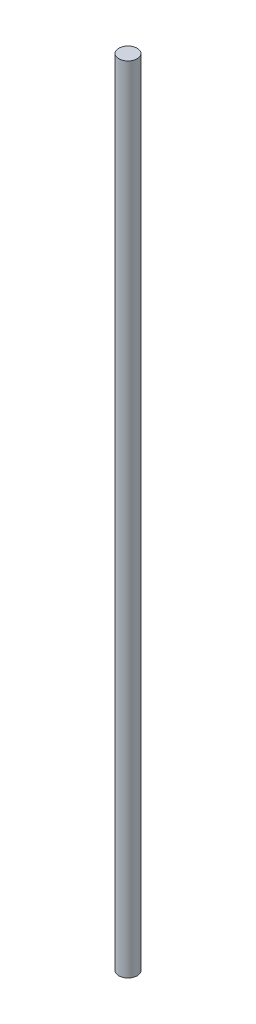
SolidWorks part; units mm, degrees
ref_plane "Plan de face" through (0, 0, 0) normal (0, 0, 1) x (1, 0, 0)
ref_plane "Plan de dessus" through (0, 0, 0) normal (0, 1, 0) x (1, 0, 0)
ref_plane "Plan de droite" through (0, 0, 0) normal (1, 0, 0) x (0, 0, -1)
sketch "Esquisse1" plane through (0, 0, 0) normal (0, 1, 0) x (1, 0, 0)
  circle A0 centre (0, 0) radius 1.5
  dimension "D1" = 3
extrude "Boss.-Extru.1" add sketch "Esquisse1" along normal blind 130
